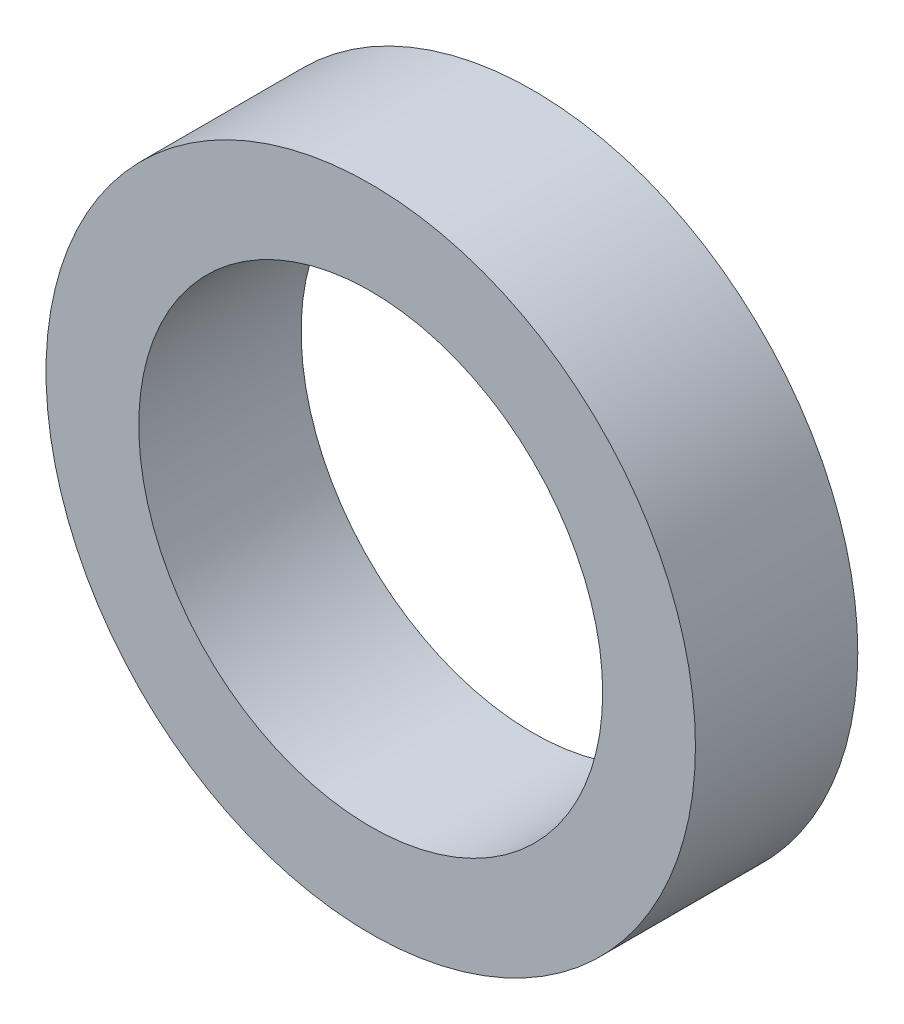
SolidWorks part; units mm, degrees
ref_plane "Front Plane" through (0, 0, 0) normal (0, 0, 1) x (1, 0, 0)
ref_plane "Top Plane" through (0, 0, 0) normal (0, 1, 0) x (1, 0, 0)
ref_plane "Right Plane" through (0, 0, 0) normal (1, 0, 0) x (0, 0, -1)
sketch "Sketch1" plane through (0, 0, 0) normal (0, 0, 1) x (1, 0, 0)
  circle A0 centre (0, 0) radius 14.2875
  circle A1 centre (0, 0) radius 20
  dimension "D1" = 28.575
  dimension "D2" = 40
extrude "Boss-Extrude1" add sketch "Sketch1" along normal blind 10
